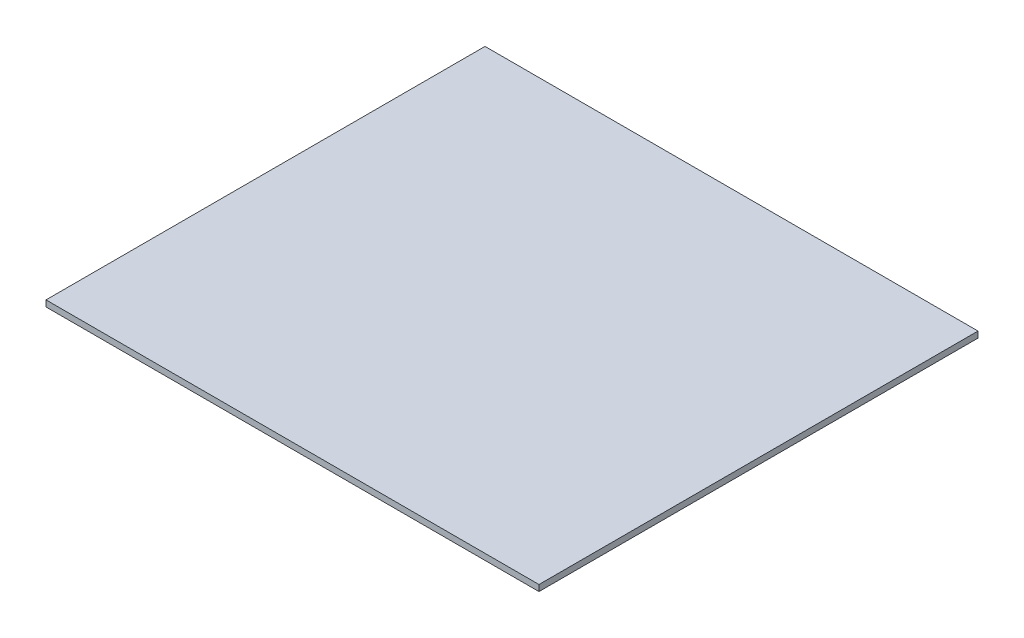
SolidWorks part; units mm, degrees
ref_plane "Front Plane" through (0, 0, 0) normal (0, 0, 1) x (1, 0, 0)
ref_plane "Top Plane" through (0, 0, 0) normal (0, 1, 0) x (1, 0, 0)
ref_plane "Right Plane" through (0, 0, 0) normal (1, 0, 0) x (0, 0, -1)
sketch "Sketch1" plane through (0, 0, 0) normal (0, 1, 0) x (1, 0, 0)
  line L1 (-64.175, 57.15) -> (64.175, 57.15)
  line L2 (-64.175, 57.15) -> (-64.175, -57.15)
  line L3 (-64.175, -57.15) -> (64.175, -57.15)
  line L4 (64.175, 57.15) -> (64.175, -57.15)
  line L5 (-64.175, 57.15) -> (64.175, -57.15) construction
  line L6 (-64.175, -57.15) -> (64.175, 57.15) construction
  point P0 (0, 0)
  dimension "D1" = 114.3
  dimension "D2" = 128.35
extrude "Boss-Extrude1" add sketch "Sketch1" along normal blind 1.6
